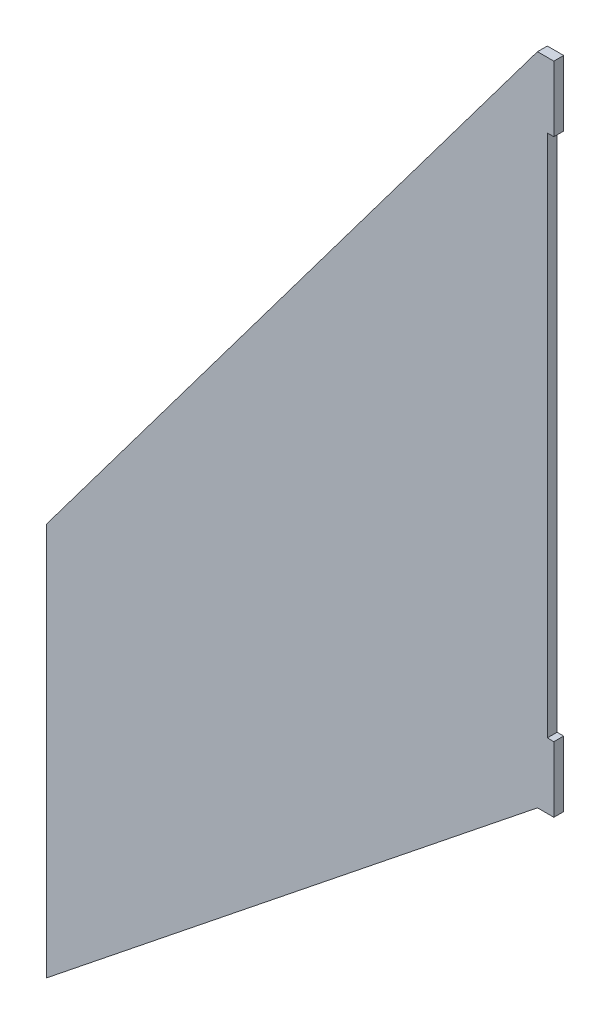
SolidWorks part; units mm, degrees
material "Alliage 1060"
ref_plane "Plan de face" through (0, 0, 0) normal (0, 0, 1) x (1, 0, 0)
ref_plane "Plan de dessus" through (0, 0, 0) normal (0, 1, 0) x (1, 0, 0)
ref_plane "Plan de droite" through (0, 0, 0) normal (1, 0, 0) x (0, 0, -1)
sketch "Esquisse1" plane through (0, 0, 0) normal (0, 0, 1) x (1, 0, 0)
  line L0 (0, 0) -> (-5, 0)
  line L1 (-5, 0) -> (-155, -200)
  line L2 (-155, -200) -> (-155, -320)
  line L3 (-155, -320) -> (-5, -200)
  line L4 (-5, -200) -> (0, -200)
  line L5 (0, -200) -> (0, -180)
  line L6 (0, -180) -> (-2, -180)
  line L7 (0, 0) -> (0, -20)
  line L8 (0, -20) -> (-2, -20)
  line L9 (-2, -20) -> (-2, -180)
  dimension "D1" = 5
  dimension "D2" = 20
  dimension "D3" = 160
  dimension "D4" = 120
  dimension "D5" = 250
  dimension "D6" = 150
  dimension "D7" = 2
  dimension "D8" = 5
  dimension "D9" = 2
extrude "Boss.-Extru.1" add sketch "Esquisse1" along normal blind 3
